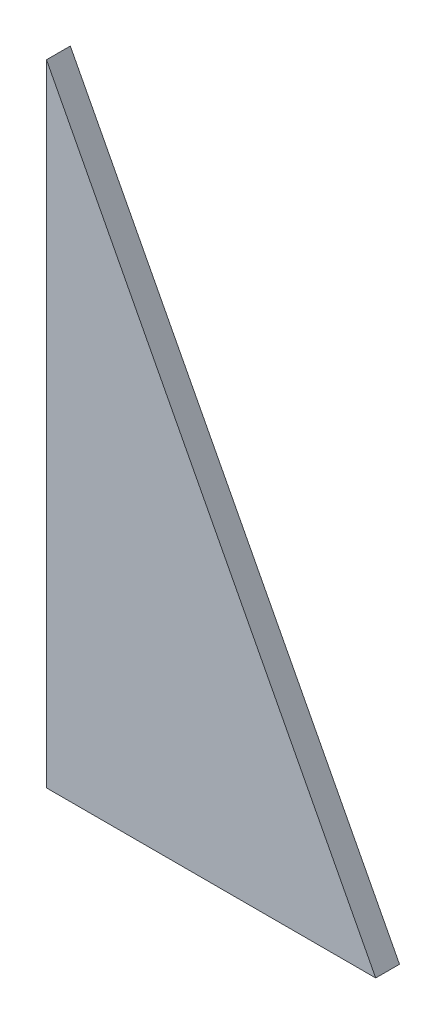
SolidWorks part; units mm, degrees
ref_plane "Ebene vorne" through (0, 0, 0) normal (0, 0, 1) x (1, 0, 0)
ref_plane "Ebene oben" through (0, 0, 0) normal (0, 1, 0) x (1, 0, 0)
ref_plane "Ebene rechts" through (0, 0, 0) normal (1, 0, 0) x (0, 0, -1)
sketch "Skizze1" plane through (0, 0, 0) normal (0, 0, 1) x (1, 0, 0)
  line L0 (0, 477) -> (0, 0)
  line L1 (0, 0) -> (249, 0)
  line L2 (249, 0) -> (0, 477)
  dimension "D1" = 0
  dimension "D2" = 477
  dimension "D3" = 0
  dimension "D4" = 249
extrude "Aufsatz-Linear austragen1" add sketch "Skizze1" along normal blind 18
